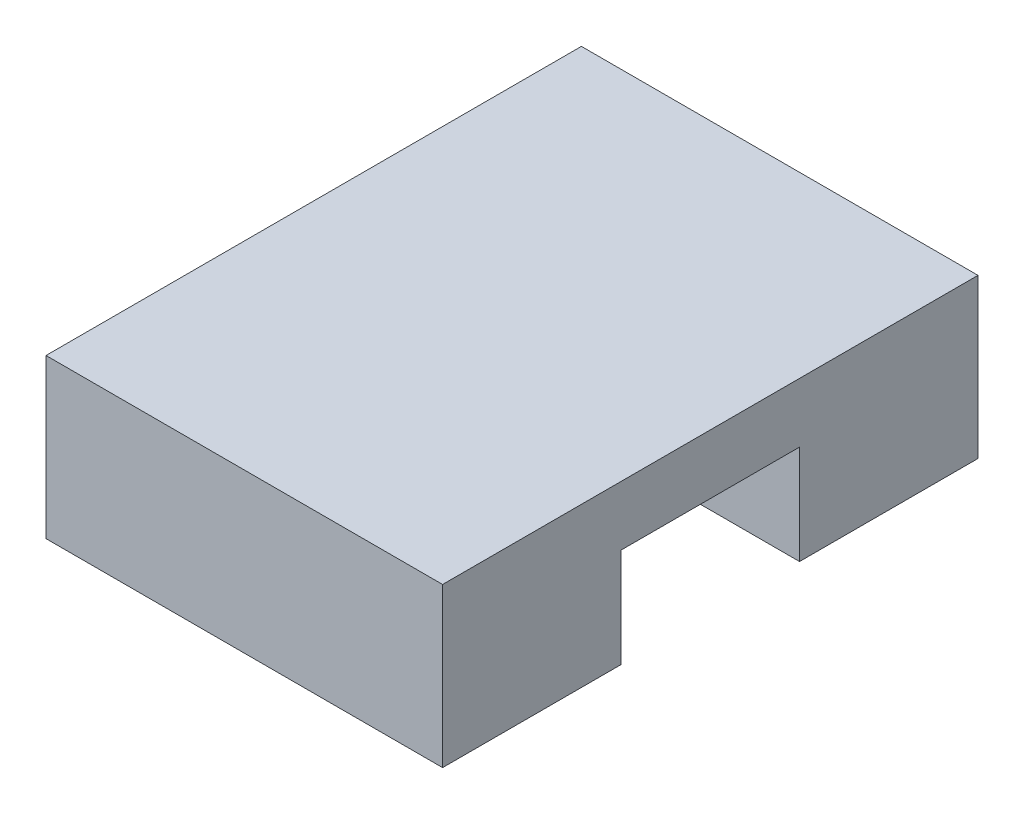
SolidWorks part; units mm, degrees
ref_plane "Front Plane" through (0, 0, 0) normal (0, 0, 1) x (1, 0, 0)
ref_plane "Top Plane" through (0, 0, 0) normal (0, 1, 0) x (1, 0, 0)
ref_plane "Right Plane" through (0, 0, 0) normal (1, 0, 0) x (0, 0, -1)
sketch "Sketch1" plane through (0, 0, 0) normal (0, 1, 0) x (1, 0, 0)
  line L1 (-20.9032, 9.871) -> (-0.9032, 9.871)
  line L2 (-20.9032, 9.871) -> (-20.9032, -17.129)
  line L3 (-20.9032, -17.129) -> (-0.9032, -17.129)
  line L4 (-0.9032, 9.871) -> (-0.9032, -17.129)
  dimension "D1" = 20
  dimension "D2" = 27
extrude "Boss-Extrude1" add sketch "Sketch1" along normal blind 8
sketch "Sketch2" plane through (-20.9032, 0, 0) normal (-1, 0, 0) x (0, 0, 1)
  line L0 (-9.871, 0) -> (17.129, 0) construction
  line L1 (-0.871, 5) -> (8.129, 5)
  line L2 (-0.871, 5) -> (-0.871, 0)
  line L3 (-0.871, 0) -> (8.129, 0)
  line L4 (8.129, 5) -> (8.129, 0)
  line L5 (-9.871, 8) -> (-9.871, 0) construction
  dimension "D3" = 9
  dimension "D1" = 9
  dimension "D2" = 5
extrude "Cut-Extrude1" cut sketch "Sketch2" against normal blind 20
equation "\"buckle_thickness\"= 8"
equation "\"visable_border\"= 3"
equation "\"cutout_border\"= 1.5"
equation "\"belt_thickness\"= 9"
equation "\"belt_width\"= 5"
equation "\"belt_placement\"= 7.5"
equation "\"base_size\"= 30"
equation "\"D1@Sketch2\"=\"belt_thickness\""
equation "\"D2@Sketch2\"=\"belt_width\""
equation "\"D3@Sketch2\"=27/2 - \"belt_thickness\"/2"
